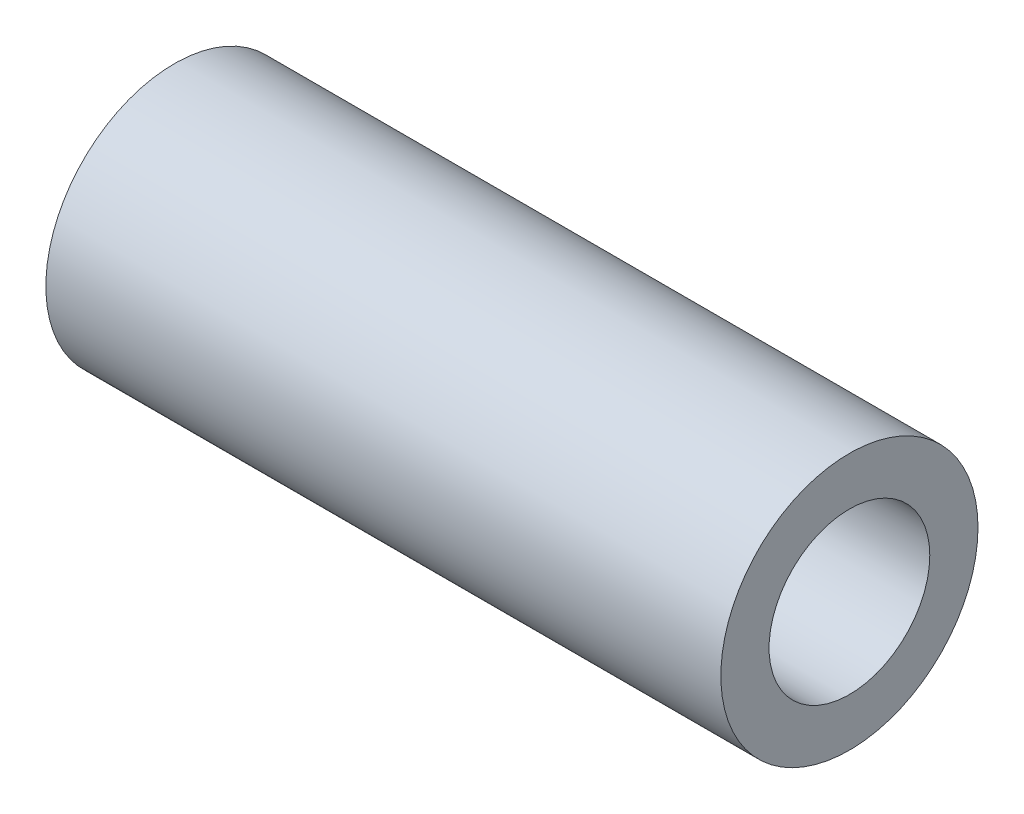
SolidWorks part; units mm, degrees
ref_plane "Front" through (0, 0, 0) normal (0, 0, 1) x (1, 0, 0)
ref_plane "Top" through (0, 0, 0) normal (0, 1, 0) x (1, 0, 0)
ref_plane "Right" through (0, 0, 0) normal (1, 0, 0) x (0, 0, -1)
sketch "Sketch1" plane through (0, 0, 0) normal (1, 0, 0) x (0, 0, -1)
  circle A0 centre (0, 0) radius 4
  circle A1 centre (0, 0) radius 2.5
  dimension "D1" = 5
  dimension "D2" = 1.5
extrude "Boss-Extrude1" add sketch "Sketch1" along normal mid plane 21
